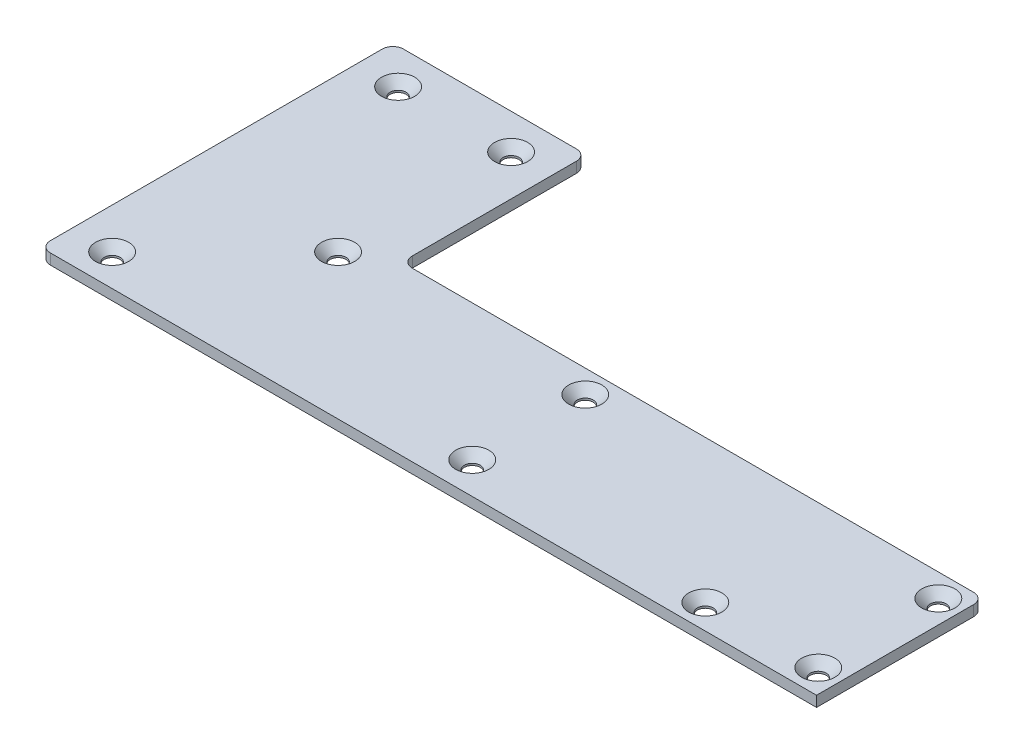
SolidWorks part; units mm, degrees
ref_plane "Front" through (0, 0, 0) normal (0, 0, 1) x (1, 0, 0)
ref_plane "Top" through (0, 0, 0) normal (0, 1, 0) x (1, 0, 0)
ref_plane "Right" through (0, 0, 0) normal (1, 0, 0) x (0, 0, -1)
sketch "Sketch1" plane through (0, 0, 0) normal (0, 1, 0) x (1, 0, 0)
  line L0 (0, 0) -> (220, 0)
  line L3 (220, 0) -> (220, 47.5)
  line L4 (220, 47.5) -> (55, 47.5)
  line L5 (55, 47.5) -> (55, 100)
  line L6 (55, 100) -> (0, 100)
  line L7 (0, 100) -> (0, 0)
  line L9 (57.5, 50) -> (337.5, 50) construction
  circle A1 centre (213.5, 7) radius 4.5 construction
  dimension "D1" = 2
  dimension "D2" = 55
  dimension "D3" = 100
  dimension "D4" = 2.5
extrude "Extrude1" add sketch "Sketch1" along normal blind 3
hole_wizard "CSK for M4 Countersunk Flat Head Screw1" positions "Sketch2" profile "Sketch3" countersink size "M4" standard "DIN" end condition up to next
sketch "Sketch2" plane through (0, 3, 0) normal (0, 1, 0) x (1, 0, 0)
  point P0 (11.5, 90)
  point P3 (11.5, 9)
  point P6 (43.5, 41)
  point P9 (43.5, 90)
  point P12 (113.5, 41)
  point P15 (113.5, 9)
  point P18 (181.5, 7)
  point P21 (213.5, 7)
  point P24 (213.5, 41)
sketch "Sketch3" plane through (11.5, 3, -90) normal (1, 0, 0) x (0, 0, 1)
  line L0 (0, 0) -> (0, 3)
  line L1 (0, 3) -> (2.25, 3)
  line L2 (2.25, 3) -> (2.25, 2.45)
  line L3 (2.25, 2.45) -> (4.7, 0)
  line L5 (4.7, 0) -> (0, 0)
  line L6 (-2.25, 2.45) -> (-4.7, 0) construction
  line L11 (0, -6.35) -> (0, 107.95) construction
  dimension "Диаметр сквозного отверстия" = 4.5
  dimension "Глубина сквозного отверстия" = 3
  dimension "Диаметр передней зенковки" = 9.4
  dimension "Угол передней зенковки" = 90
fillet "Fillet1" radius 3 5 edges at (220, 1.5, -47.5) (0, 1.5, 0) (0, 1.5, -100) (55, 1.5, -47.5) (55, 1.5, -100)
